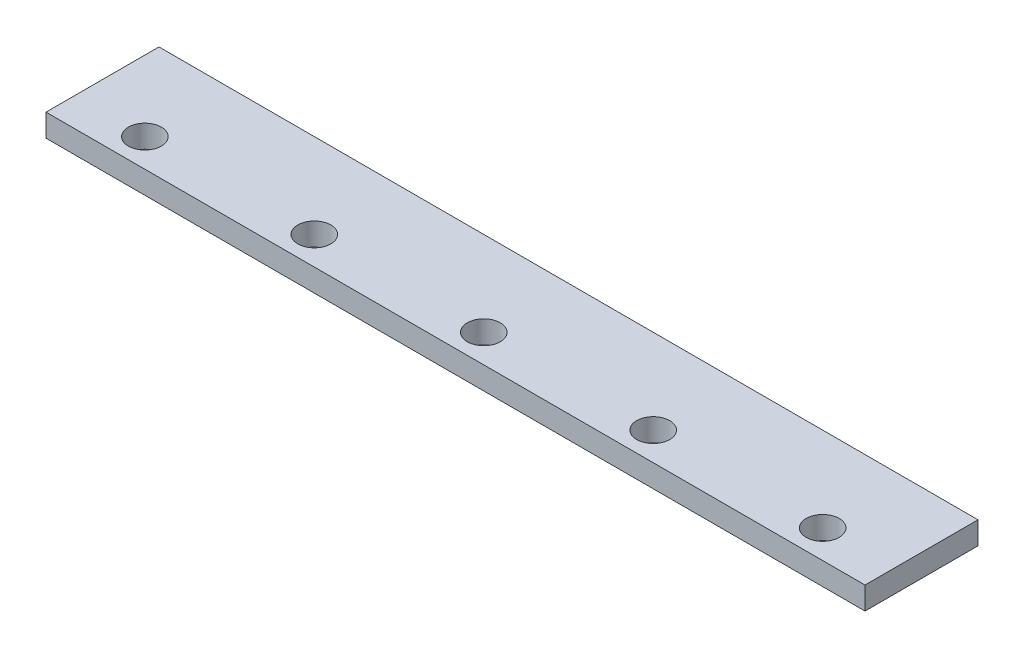
SolidWorks part; units mm, degrees
ref_plane "Front Plane" through (0, 0, 0) normal (0, 0, 1) x (1, 0, 0)
ref_plane "Top Plane" through (0, 0, 0) normal (0, 1, 0) x (1, 0, 0)
ref_plane "Right Plane" through (0, 0, 0) normal (1, 0, 0) x (0, 0, -1)
sketch "Sketch2" plane through (0, 0, 0) normal (0, 1, 0) x (1, 0, 0)
  line L1 (0, 0) -> (580, 0)
  line L2 (0, 0) -> (0, 80)
  line L3 (0, 80) -> (580, 80)
  line L4 (580, 0) -> (580, 80)
  dimension "D1" = 580
  dimension "D2" = 80
extrude "Boss-Extrude1" add sketch "Sketch2" along normal blind 16
sketch "Sketch3" plane through (0, 16, 0) normal (0, 1, 0) x (1, 0, 0)
  line L0 (0, 0) -> (580, 0) construction
  circle A0 centre (50, 20) radius 11.6692
  circle A1 centre (170, 20) radius 11.6692
  circle A2 centre (290, 20) radius 11.6692
  circle A3 centre (410, 20) radius 11.6692
  circle A4 centre (530, 20) radius 11.6692
  dimension "D3" = 5
  dimension "D1" = 20
  dimension "D2" = 50
extrude "Cut-Extrude1" cut sketch "Sketch3" against normal blind 16
